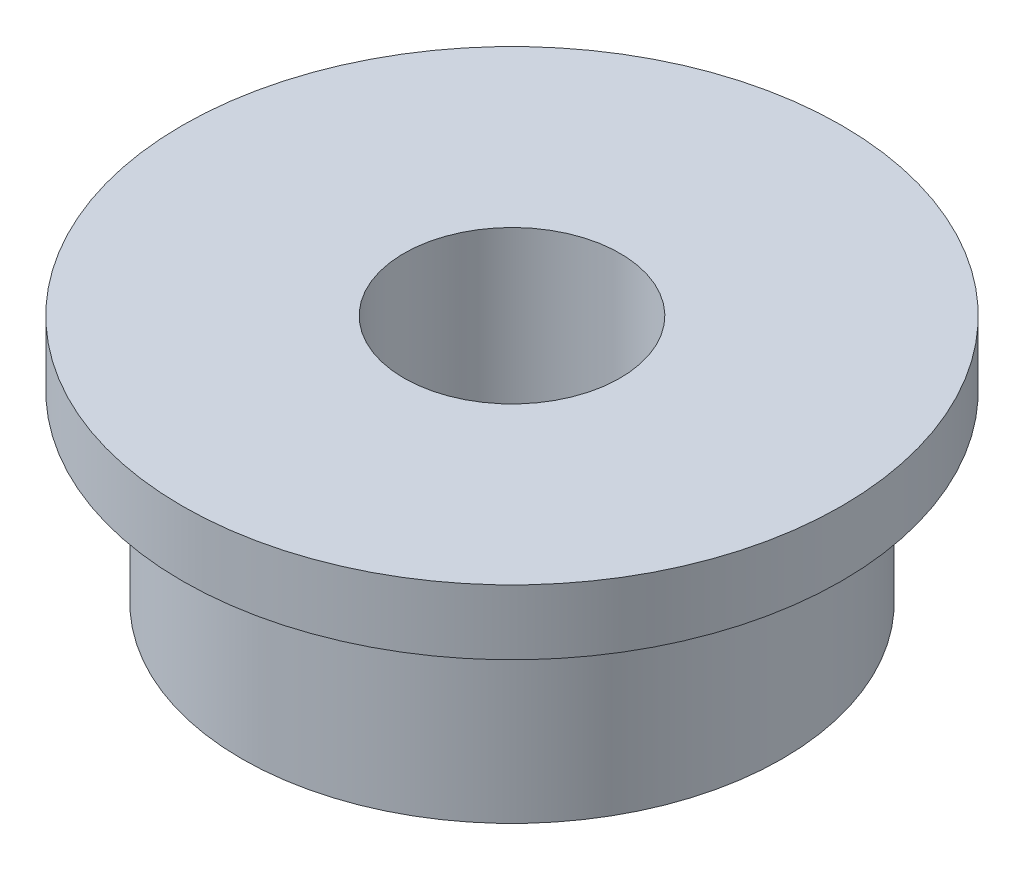
SolidWorks part; units mm, degrees
ref_plane "Front Plane" through (0, 0, 0) normal (0, 0, 1) x (1, 0, 0)
ref_plane "Top Plane" through (0, 0, 0) normal (0, 1, 0) x (1, 0, 0)
ref_plane "Right Plane" through (0, 0, 0) normal (1, 0, 0) x (0, 0, -1)
sketch "Sketch1" plane through (0, 0, 0) normal (0, 1, 0) x (1, 0, 0)
  circle A0 centre (0, 0) radius 2.5
  circle A1 centre (0, 0) radius 1
  dimension "D1" = 2
  dimension "D2" = 5
extrude "Boss-Extrude1" add sketch "Sketch1" along normal blind 2.3
sketch "Sketch2" plane through (0, 2.3, 0) normal (0, 1, 0) x (1, 0, 0)
  circle A0 centre (0, 0) radius 3.05
  circle A1 centre (0, 0) radius 1
  dimension "D1" = 6.1
extrude "Boss-Extrude2" add sketch "Sketch2" against normal blind 0.6
